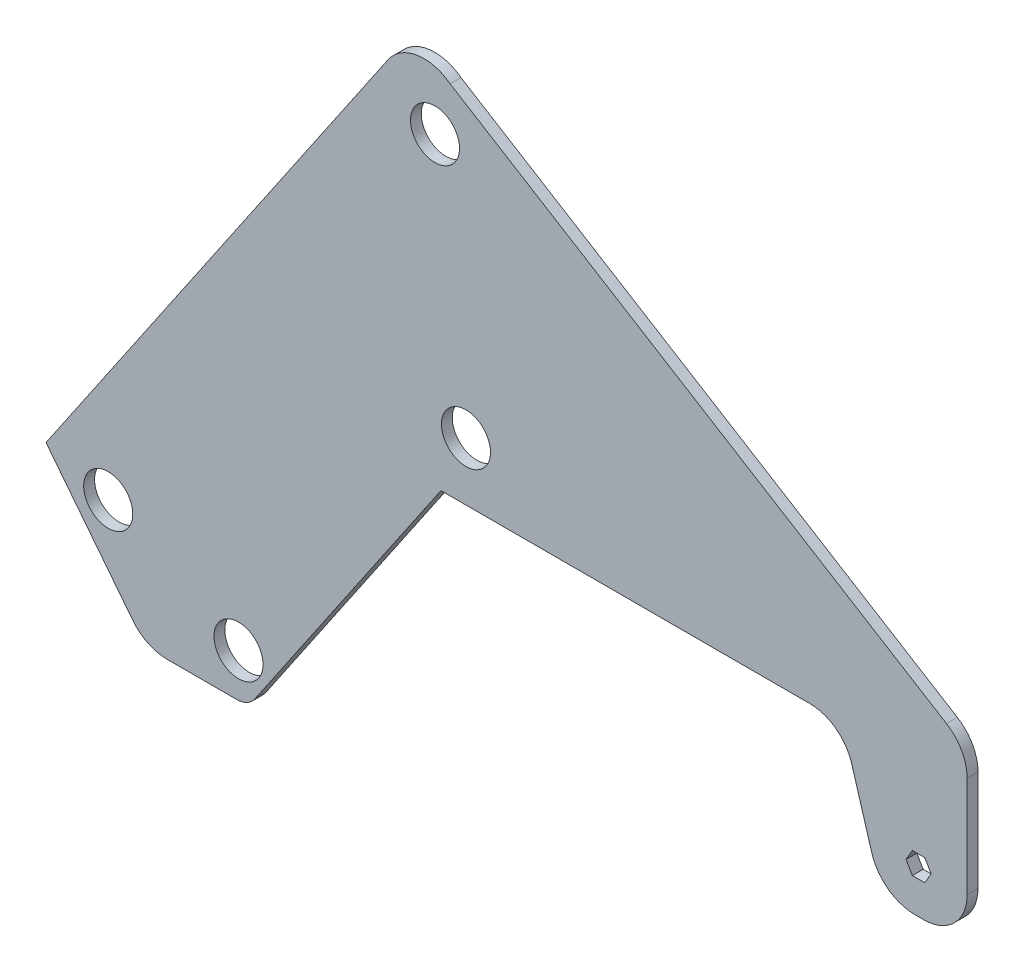
SolidWorks part; units mm, degrees
other "Markup1"
sketch "Sketch1" plane through (-441.7893, 331.8239, 6.35) normal (-0.0431, 0.0102, 0.999) x (0.9985, 0.0354, 0.0427)
sketch "Sketch2" plane through (-413.6701, 343.933, 6.35) normal (-0.0431, 0.0102, 0.999) x (0.9985, 0.0354, 0.0427)
sketch "Sketch3" plane through (-436.3774, 318.5567, 6.35) normal (-0.0431, 0.0102, 0.999) x (0.9985, 0.0354, 0.0427)
sketch "Sketch5" plane through (-436.3774, 318.5567, 6.35) normal (-0.0431, 0.0102, 0.999) x (0.9985, 0.0354, 0.0427)
sketch "Sketch7" plane through (-436.3774, 318.5567, 6.35) normal (-0.0431, 0.0102, 0.999) x (0.9985, 0.0354, 0.0427)
other "Markup2"
sketch "Sketch4" plane through (102.4721, 318.5567, 6.35) normal (0.9364, 0.1073, 0.3342) x (0.3416, -0.0598, -0.9379)
sketch "Sketch6" plane through (102.4721, 318.5567, 6.35) normal (0.9364, 0.1073, 0.3342) x (0.3416, -0.0598, -0.9379)
sketch "Sketch8" plane through (102.4721, 318.5567, 6.35) normal (0.9364, 0.1073, 0.3342) x (0.3416, -0.0598, -0.9379)
ref_plane "Front Plane" through (0, 0, 0) normal (0, 0, 1) x (1, 0, 0)
ref_plane "Top Plane" through (0, 0, 0) normal (0, 1, 0) x (1, 0, 0)
ref_plane "Right Plane" through (0, 0, 0) normal (1, 0, 0) x (0, 0, -1)
sketch "Model" plane through (0, 0, 0) normal (0, 0, 1) x (1, 0, 0)
  line L1 (-205.3388, 104.6502) -> (-2.1388, 104.6502)
  line L3 (-314.2383, -55.3595) -> (-205.3388, 104.6502)
  line L4 (-236.3032, 307.4477) -> (-436.3774, 13.472)
  line L5 (-436.3774, 13.472) -> (-385.5815, -51.2028)
  line L13 (81.3935, 53.8502) -> (77.7274, 60.2002)
  line L14 (77.7274, 60.2002) -> (70.395, 60.2002)
  line L15 (70.395, 60.2002) -> (66.7288, 53.8502)
  line L16 (66.7288, 53.8502) -> (70.395, 47.5002)
  line L17 (70.395, 47.5002) -> (77.7274, 47.5002)
  line L18 (77.7274, 47.5002) -> (81.3935, 53.8502)
  line L19 (-365.606, -60.914) -> (-324.7375, -60.914)
  line L20 (-871.0211, -88.854) -> (370.1019, -88.854) construction
  line L22 (102.4721, 53.8502) -> (102.4721, 83.8724)
  line L27 (71.8831, 28.4502) -> (77.0721, 28.4502)
  line L28 (-399.9752, 2.586) -> (-323.7752, -35.514) construction
  line L29 (-323.7752, -35.514) -> (-190.7071, 138.5169) construction
  line L30 (-190.7071, 138.5169) -> (-208.8329, 283.4378) construction
  line L31 (-208.8329, 283.4378) -> (-399.9752, 2.586) construction
  line L32 (46.5921, 47.5002) -> (34.8921, 86.5418)
  line L33 (10.5612, 104.6502) -> (-11.3966, 104.6502)
  line L34 (102.4721, 83.8724) -> (102.4721, 112.8538)
  line L35 (90.397, 134.478) -> (-199.9496, 313.3896)
  circle A9 centre (-323.7752, -35.514) radius 14.351
  circle A10 centre (-399.9752, 2.586) radius 14.351
  circle A12 centre (-190.7071, 138.5169) radius 14.351
  circle A22 centre (-208.8329, 283.4378) radius 14.351
  circle A24 centre (74.0612, 53.8502) radius 6.35 construction
  arc A31 (-324.7375, -60.914) -> (-314.2383, -55.3595) centre (-324.7375, -48.214) ccw
  arc A40 (46.5921, 47.5002) -> (71.8831, 28.4502) centre (71.8831, 54.7636) ccw
  arc A43 (77.0721, 28.4502) -> (102.4721, 53.8502) centre (77.0721, 53.8502) ccw
  arc A44 (-236.3032, 307.4477) -> (-199.9496, 313.3896) centre (-215.305, 293.1567) cw
  arc A45 (-365.606, -60.914) -> (-385.5815, -51.2028) centre (-365.606, -35.514) cw
  arc A46 (34.8921, 86.5418) -> (10.5612, 104.6502) centre (10.5612, 79.2502) ccw
  arc A47 (102.4721, 112.8538) -> (90.397, 134.478) centre (77.0721, 112.8538) ccw
  point P8 (46.5921, 47.5002)
  point P9 (-271.8415, 170.8089)
  point P31 (-221.2548, 329.5588)
  point P34 (100.2935, -12.8222)
  point P43 (-377.9543, -60.914)
  point P59 (174.831, 53.8502)
  dimension "D3" = 38.1
  dimension "D4" = 104.6502
  dimension "D5" = 76.2
  dimension "D6" = 25.4
  dimension "D7" = 12.7
  dimension "D8" = 28.702
  dimension "D11" = 139.7
  dimension "D12" = 27.94
  dimension "D21" = 124.238
  dimension "D13" = 12.7
  dimension "D16" = 355.6
  dimension "D23" = 25.4
  dimension "D24" = 25.4
  dimension "D26" = 26.3134
  dimension "D14" = 406.4
  dimension "D20" = 215.9
  dimension "D29" = 25.4
  dimension "D31" = 25.4
  dimension "D25" = 88.9
  dimension "D9" = 19.05
  dimension "D10" = 146.05
  dimension "D15" = 33.8667
  dimension "D17" = 339.725
  dimension "D18" = 219.075
  dimension "D19" = 50.8
  dimension "D22" = 25.4
  dimension "D27" = 53.2168
  dimension "D28" = 25.4
  dimension "D30" = 55.88
extrude "Boss-Extrude1" add sketch "Model" along normal blind 6.35
